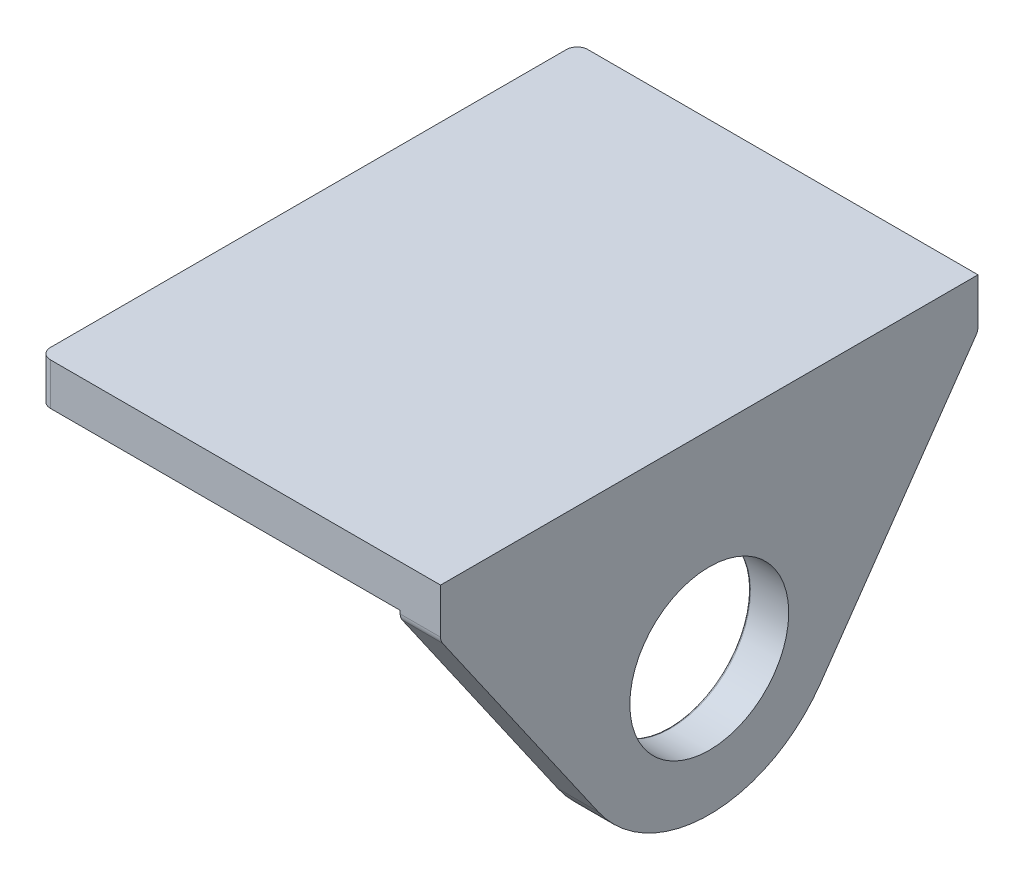
SolidWorks part; units mm, degrees
material "6061-T6 (SS)"
ref_plane "Front Plane" through (0, 0, 0) normal (0, 0, 1) x (1, 0, 0)
ref_plane "Top Plane" through (0, 0, 0) normal (0, 1, 0) x (1, 0, 0)
ref_plane "Right Plane" through (0, 0, 0) normal (1, 0, 0) x (0, 0, -1)
sketch "Sketch1" plane through (0, 0, 0) normal (0, 1, 0) x (1, 0, 0)
  line L0 (42.6466, 63.5762) -> (42.6466, 0) construction
  line L1 (0, 0) -> (47.4218, 0)
  line L2 (0, 0) -> (0, 63.5762)
  line L3 (0, 63.5762) -> (47.4218, 63.5762)
  line L4 (47.4218, 0) -> (47.4218, 63.5762)
  dimension "D1" = 63.5762
  dimension "D2" = 47.4218
  dimension "D3" = 4.7752
extrude "Boss-Extrude1" add sketch "Sketch1" along normal blind 4.9784
sketch "Sketch3" plane through (0, 0, 0) normal (0, -1, 0) x (1, 0, 0)
  line L0 (47.4218, -63.5762) -> (0, -63.5762) construction
  line L4 (47.4218, 0) -> (42.6466, 0)
  line L5 (47.4218, 0) -> (47.4218, -63.5762)
  line L6 (47.4218, -63.5762) -> (42.6466, -63.5762)
  line L7 (42.6466, 0) -> (42.6466, -63.5762)
  dimension "D1" = 4.7752
extrude "Boss-Extrude2" add sketch "Sketch3" along normal blind 34.4424
sketch "Sketch4" plane through (42.6466, 0, 0) normal (-1, 0, 0) x (0, 0, 1)
  line L1 (0, -34.4424) -> (-63.5762, -34.4424) construction
  line L3 (-63.5762, 0) -> (-63.5762, -0.762)
  line L4 (-63.5762, -34.4424) -> (-63.5762, 0) construction
  line L5 (0, 0) -> (0, -0.762)
  line L6 (0, -34.4424) -> (0, 0) construction
  line L7 (0, -0.762) -> (-18.6513, -27.5776)
  line L8 (-63.5762, -0.762) -> (-44.9249, -27.5776)
  line L10 (0, -34.4424) -> (-63.5762, -34.4424)
  line L11 (0, -34.4424) -> (0, 0)
  line L12 (0, 0) -> (-63.5762, 0)
  line L13 (-63.5762, -34.4424) -> (-63.5762, 0)
  circle A0 centre (-31.7881, -18.4404) radius 9.398
  arc A1 (-44.9249, -27.5776) -> (-18.6513, -27.5776) centre (-31.7881, -18.4404) ccw
  point P5 (-31.7881, -34.4424)
  line M5 (-63.5762, 0) -> (-63.5762, -34.4424)
  line M6 (-63.5762, -34.4424) -> (0, -34.4424)
  line M7 (0, -34.4424) -> (0, 0)
  dimension "D1" = 18.796
  dimension "D2" = 32.004
  dimension "D3" = 0.762
  dimension "D4" = 0.762
extrude "Cut-Extrude1" cut sketch "Sketch4" against normal through all contours A1 L10 L7 M7 | A1 L8 M5 M6 | A0
fillet "Fillet1" radius 1.27 2 edges at (45.0342, -0.762, -63.5762) (45.0342, -0.762, 0)
fillet "Fillet2" radius 1.27 2 edges at (0, 2.4892, -63.5762) (0, 2.4892, 0)
fillet "Fillet3" radius 0.254 1 edges at (42.6466, -18.4404, -22.3901)
